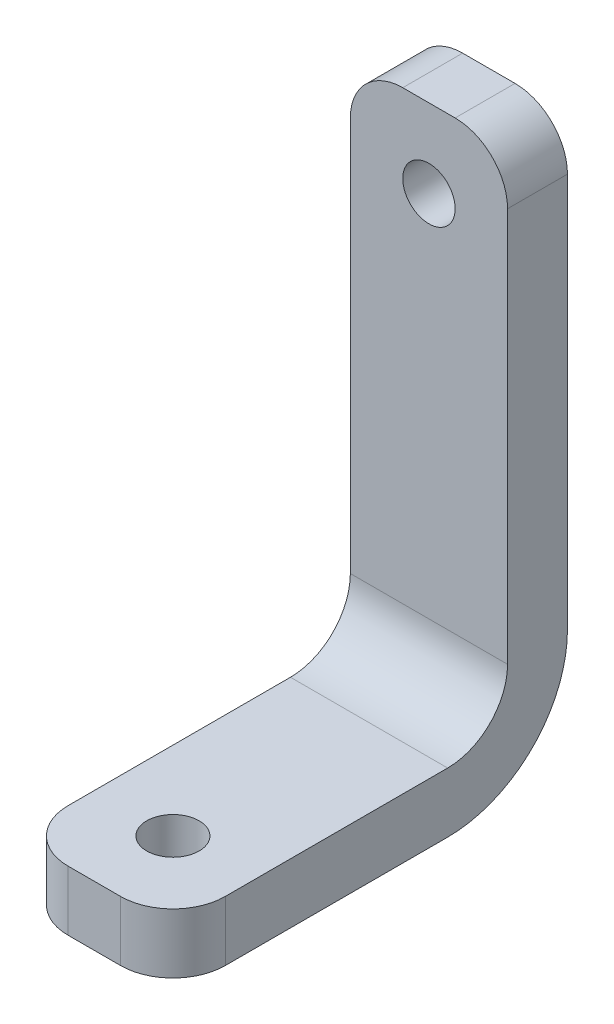
SolidWorks part; units mm, degrees
ref_plane "Plan de face" through (0, 0, 0) normal (0, 0, 1) x (1, 0, 0)
ref_plane "Plan de dessus" through (0, 0, 0) normal (0, 1, 0) x (1, 0, 0)
ref_plane "Plan de droite" through (0, 0, 0) normal (1, 0, 0) x (0, 0, -1)
sketch "Esquisse1" plane through (0, 0, 0) normal (0, 0, 1) x (1, 0, 0)
  line L0 (0, 11.925) -> (0, 15.425) construction
  line L1 (-5.25, 18.925) -> (5.25, 18.925)
  line L2 (-5.25, 18.925) -> (-5.25, -18.925)
  line L3 (-5.25, -18.925) -> (5.25, -18.925)
  line L4 (5.25, 18.925) -> (5.25, -18.925)
  line L5 (0, 15.425) -> (0, 18.925) construction
  line L7 (1.75, 13.675) -> (-1.75, 13.675) construction
  line L8 (-1.75, 13.675) -> (-5.25, 13.675) construction
  circle A0 centre (0, 13.675) radius 1.75
  point P4 (0, 18.925)
  point P6 (-5.25, 0)
  dimension "D3" = 3.5
  dimension "D1" = 32.6
extrude "Boss.-Extru.1" add sketch "Esquisse1" along normal blind 4
sketch "Esquisse2" plane through (0, 0, 4) normal (0, 0, 1) x (1, 0, 0)
  line L0 (-5.25, 18.925) -> (-5.25, -18.925) construction
  line L1 (-5.25, -18.925) -> (5.25, -18.925)
  line L2 (-5.25, -18.925) -> (-5.25, -14.925)
  line L3 (-5.25, -14.925) -> (5.25, -14.925)
  line L4 (5.25, -18.925) -> (5.25, -14.925)
  line L5 (-5.25, -18.925) -> (5.25, -18.925) construction
  dimension "D1" = 4
extrude "Boss.-Extru.2" add sketch "Esquisse2" along normal blind 22.35
sketch "Esquisse3" plane through (0, -18.925, 0) normal (0, -1, 0) x (1, 0, 0)
  line L0 (0, 0) -> (0, 21.1) construction
  line L1 (-5.25, 0) -> (5.25, 0) construction
  circle A0 centre (0, 21.1) radius 1.75
  dimension "D1" = 3.5
  dimension "D2" = 21.1
extrude "Enlèv. mat.-Extru.1" cut sketch "Esquisse3" against normal up to next
fillet "Congé1" radius 3.5 4 edges at (-5.25, -16.925, 26.35) (5.25, -16.925, 26.35) (-5.25, 18.925, 2) (5.25, 18.925, 2)
fillet "Congé2" radius 4 1 edges at (0, -14.925, 4)
fillet "Congé3" radius 8 1 edges at (0, -18.925, 0)
